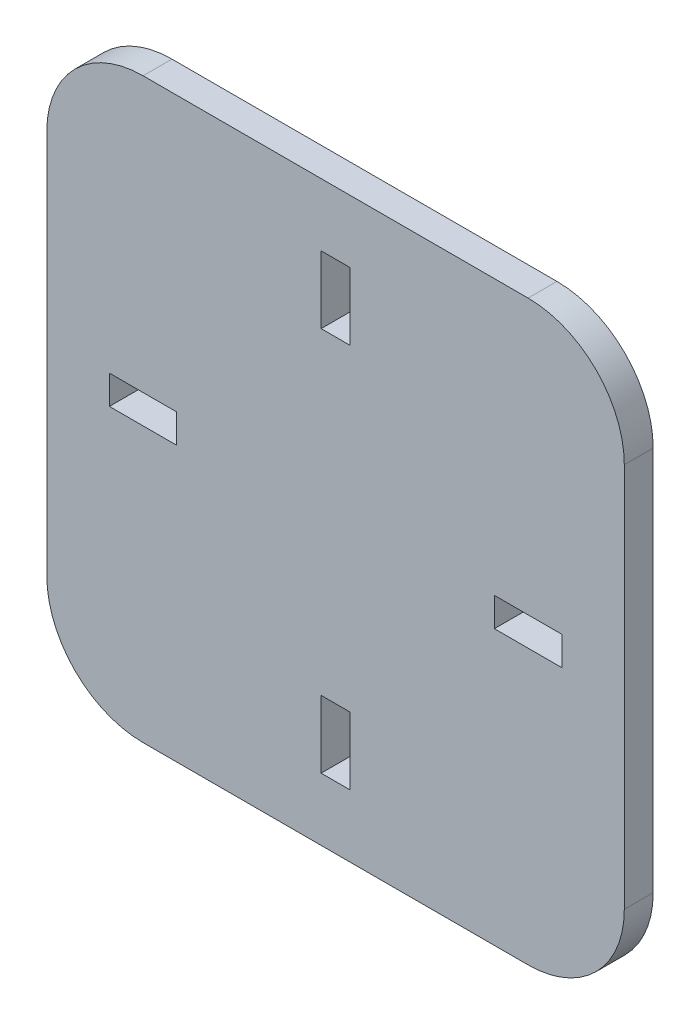
SolidWorks part; units mm, degrees
ref_plane "Plano frontal" through (0, 0, 0) normal (0, 0, 1) x (1, 0, 0)
ref_plane "Plano superior" through (0, 0, 0) normal (0, 1, 0) x (1, 0, 0)
ref_plane "Plano direito" through (0, 0, 0) normal (1, 0, 0) x (0, 0, -1)
sketch "Esboço1" plane through (0, 0, 0) normal (0, 0, 1) x (1, 0, 0)
  line L1 (-30, -30) -> (30, -30)
  line L2 (-30, -30) -> (-30, 30)
  line L3 (-30, 30) -> (30, 30)
  line L4 (30, -30) -> (30, 30)
  line L5 (-30, -30) -> (30, 30) construction
  line L6 (-30, 30) -> (30, -30) construction
  point P0 (0, 0)
  dimension "D1" = 90
  dimension "D2" = 60
  dimension "D3" = 60
extrude "Ressalto-extrusão1" add sketch "Esboço1" along normal blind 3
sketch "Esboço2" plane through (0, 0, 3) normal (0, 0, 1) x (1, 0, 0)
  line L5 (16.5, 1.5) -> (23.5, 1.5)
  line L6 (16.5, 1.5) -> (16.5, -1.5)
  line L18 (16.5, -1.5) -> (23.5, -1.5)
  line L19 (23.5, 1.5) -> (23.5, -1.5)
  line L20 (1.5, -16.5) -> (1.5, -23.5)
  line L21 (1.5, -16.5) -> (-1.5, -16.5)
  line L26 (-1.5, -16.5) -> (-1.5, -23.5)
  line L27 (1.5, -23.5) -> (-1.5, -23.5)
  line L32 (-16.5, -1.5) -> (-23.5, -1.5)
  line L33 (-16.5, -1.5) -> (-16.5, 1.5)
  line L38 (-16.5, 1.5) -> (-23.5, 1.5)
  line L39 (-23.5, -1.5) -> (-23.5, 1.5)
  line L41 (-1.5, 16.5) -> (1.5, 16.5)
  line L42 (-1.5, 16.5) -> (-1.5, 23.5)
  line L43 (-1.5, 23.5) -> (1.5, 23.5)
  line L44 (1.5, 16.5) -> (1.5, 23.5)
  line L45 (-1.5, 16.5) -> (1.5, 23.5) construction
  line L46 (-1.5, 23.5) -> (1.5, 16.5) construction
  circle A0 centre (0, 0) radius 20 construction
  point P2 (0, 0)
  point P17 (0, 0)
  point P23 (0, 0)
  point P54 (0, 20)
  dimension "D4" = 4
  dimension "D3" = 23.5
  dimension "D1" = 7
  dimension "D2" = 3
extrude "Corte-extrusão1" cut sketch "Esboço2" against normal blind 3
fillet "Filete1" radius 10 4 edges at (-30, 30, 1.5) (30, 30, 1.5) (30, -30, 1.5) (-30, -30, 1.5)
